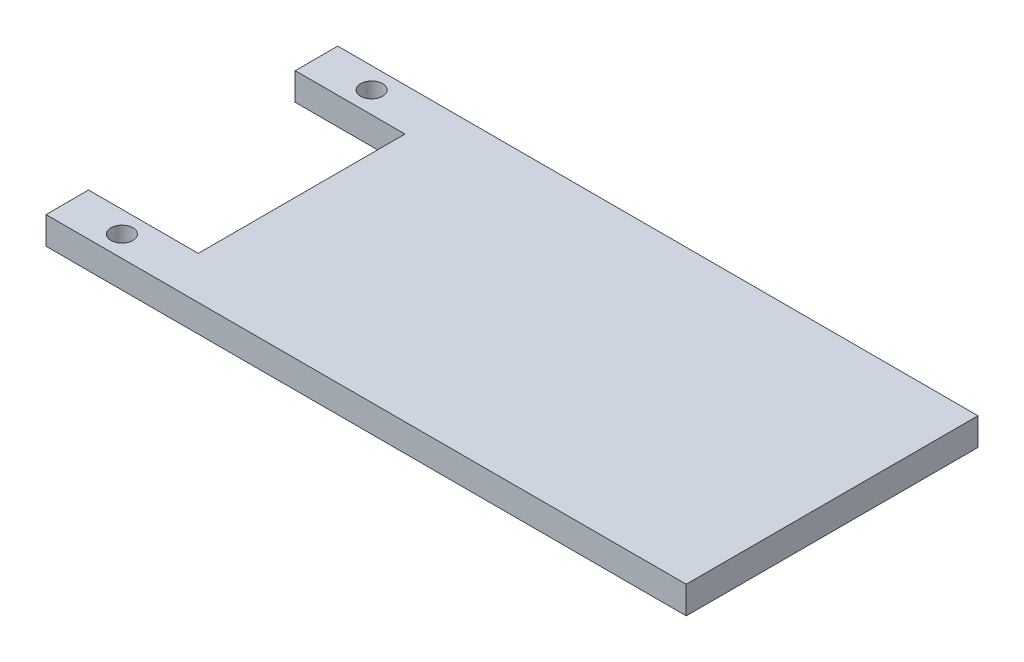
SolidWorks part; units mm, degrees
ref_plane "Front Plane" through (0, 0, 0) normal (0, 0, 1) x (1, 0, 0)
ref_plane "Top Plane" through (0, 0, 0) normal (0, 1, 0) x (1, 0, 0)
ref_plane "Right Plane" through (0, 0, 0) normal (1, 0, 0) x (0, 0, -1)
sketch "Sketch1" plane through (0, 0, 0) normal (0, 1, 0) x (1, 0, 0)
  line L1 (-35, -15.95) -> (35, -15.95)
  line L2 (-35, -15.95) -> (-35, 15.95)
  line L3 (-35, 15.95) -> (35, 15.95)
  line L4 (35, -15.95) -> (35, 15.95)
  line L5 (0, 15.95) -> (0, -15.95) construction
  line L6 (-35, 0) -> (35, 0) construction
  point P0 (0, 0)
  dimension "D1" = 31.9
  dimension "D2" = 70
extrude "Boss-Extrude1" add sketch "Sketch1" along normal blind 3
sketch "Sketch2" plane through (0, 3, 0) normal (0, 1, 0) x (1, 0, 0)
  line L0 (-29, -15.95) -> (-29, 15.95) construction
  line L1 (-35, -15.95) -> (35, -15.95) construction
  line L2 (35, 15.95) -> (-35, 15.95) construction
  line L3 (-35, 15.95) -> (-35, -15.95) construction
  circle A0 centre (-29, 13.65) radius 1.2
  dimension "D1" = 2.4
  dimension "D2" = 2.3
  dimension "D3" = 6
extrude "Cut-Extrude1" cut sketch "Sketch2" against normal blind 3
mirror "Mirror1" about plane through (0, 0, 0) normal (0, 0, 1) of "Cut-Extrude1"
sketch "Sketch3" plane through (0, 3, 0) normal (0, 1, 0) x (1, 0, 0)
  line L0 (35, 0) -> (-35, 0) construction
  line L1 (35, -15.95) -> (35, 15.95) construction
  line L2 (-35, 15.95) -> (-35, -15.95) construction
  line L4 (-47, -11.3) -> (-23, -11.3)
  line L5 (-47, -11.3) -> (-47, 11.3)
  line L6 (-47, 11.3) -> (-23, 11.3)
  line L7 (-23, -11.3) -> (-23, 11.3)
  line L8 (-35, 11.3) -> (-35, -11.3) construction
  line L9 (-47, 0) -> (-23, 0) construction
  dimension "D1" = 22.6
  dimension "D2" = 12
extrude "Cut-Extrude2" cut sketch "Sketch3" against normal blind 3
